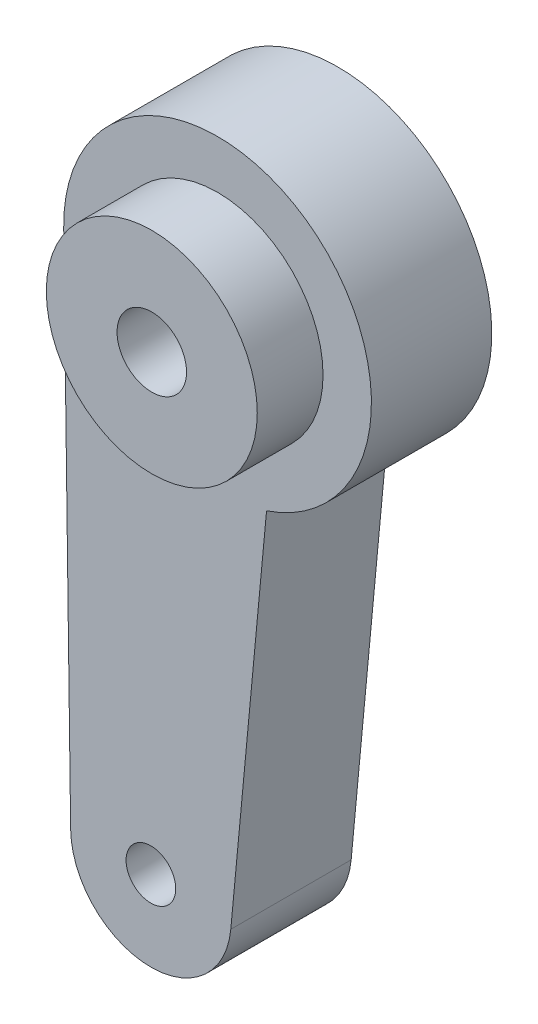
SolidWorks part; units mm, degrees
ref_plane "Plano frontal" through (0, 0, 0) normal (0, 0, 1) x (1, 0, 0)
ref_plane "Plano superior" through (0, 0, 0) normal (0, 1, 0) x (1, 0, 0)
ref_plane "Plano direito" through (0, 0, 0) normal (1, 0, 0) x (0, 0, -1)
sketch "Esboço1" plane through (0, 0, 0) normal (0, 0, 1) x (1, 0, 0)
  line L1 (-12.398, -0.1664) -> (-11.8381, -41.8803)
  line L2 (3.9483, -11.7536) -> (1.0663, -42.399)
  circle A0 centre (0, 0) radius 5.5
  arc A1 (1.0663, -42.399) -> (-11.8381, -41.8803) centre (-5.372, -41.7935) cw
  circle A6 centre (-5.372, -41.7935) radius 2
  arc A7 (-12.398, -0.1664) -> (3.9483, -11.7536) centre (0, 0) cw
extrude "Ressalto-extrusão1" add sketch "Esboço1" along normal blind 9.7
sketch "Esboço2" plane through (0, 0, 9.7) normal (0, 0, 1) x (1, 0, 0)
  circle A0 centre (0, 0) radius 2.8
  circle A1 centre (0, 0) radius 8.5
extrude "Ressalto-extrusão2" add sketch "Esboço2" along normal blind 5.3
